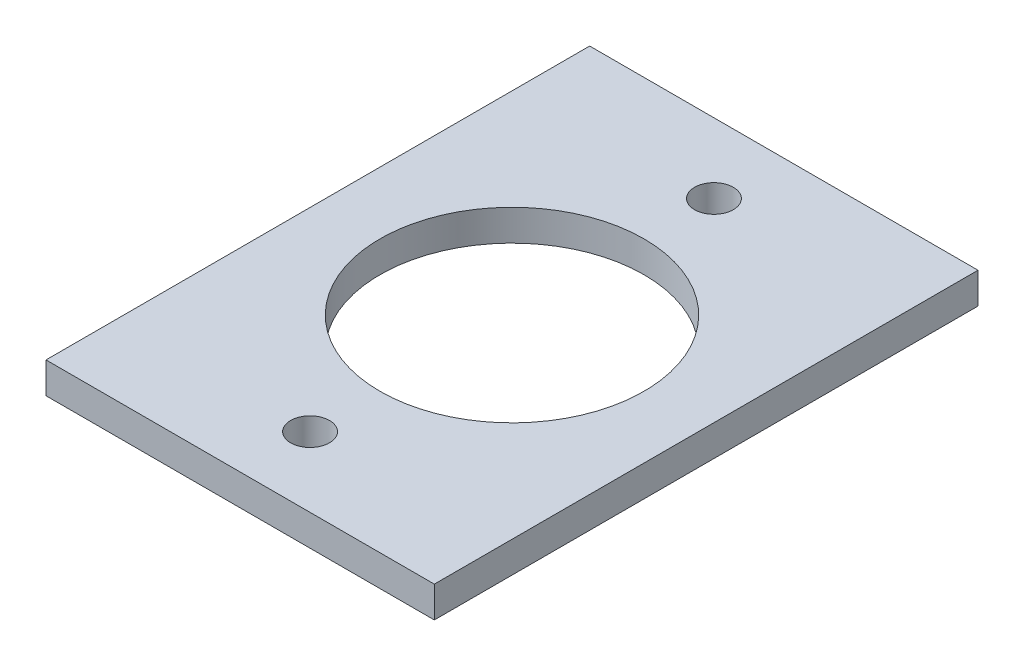
SolidWorks part; units mm, degrees
ref_plane "정면" through (0, 0, 0) normal (0, 0, 1) x (1, 0, 0)
ref_plane "윗면" through (0, 0, 0) normal (0, 1, 0) x (1, 0, 0)
ref_plane "우측면" through (0, 0, 0) normal (1, 0, 0) x (0, 0, -1)
sketch "스케치1" plane through (0, 0, 0) normal (0, 1, 0) x (1, 0, 0)
  line L1 (12.5, -17.5) -> (-12.5, -17.5)
  line L2 (12.5, -17.5) -> (12.5, 17.5)
  line L3 (12.5, 17.5) -> (-12.5, 17.5)
  line L4 (-12.5, -17.5) -> (-12.5, 17.5)
  line L5 (12.5, -17.5) -> (-12.5, 17.5) construction
  line L6 (12.5, 17.5) -> (-12.5, -17.5) construction
  circle A0 centre (0, 0) radius 8.5
  dimension "D1" = 17
  dimension "D3" = 25
  dimension "D4" = 35
extrude "보스-돌출4" add sketch "스케치1" along normal blind 2
sketch "스케치8" plane through (0, 2, 0) normal (0, 1, 0) x (1, 0, 0)
  line L0 (0, 0) -> (0, 13) construction
  dimension "D1" = 13
hole_wizard "M3 탭을 위한 탭 드릴1" positions "스케치13" profile "스케치14" hole size "M3" standard "ISO" end condition through all
sketch "스케치13" plane through (0, 2, 0) normal (0, 1, 0) x (1, 0, 0)
  point P0 (0, 13)
sketch "스케치14" plane through (0, 2, -13) normal (1, 0, 0) x (0, 0, 1)
  line L0 (0, 0) -> (0, 2)
  line L1 (0, 2) -> (1.25, 2)
  line L2 (1.25, 2) -> (1.25, 0)
  line L5 (1.25, 0) -> (0, 0)
  line L11 (0, -6.35) -> (0, 107.95) construction
  dimension "관통 구멍 지름" = 2.5
  dimension "관통 구멍 깊이" = 2
pattern_circular "원형 패턴1" count 2 over 360 about axis through (0, 0, 0) along (0, 1, 0) of "M3 탭을 위한 탭 드릴1"
